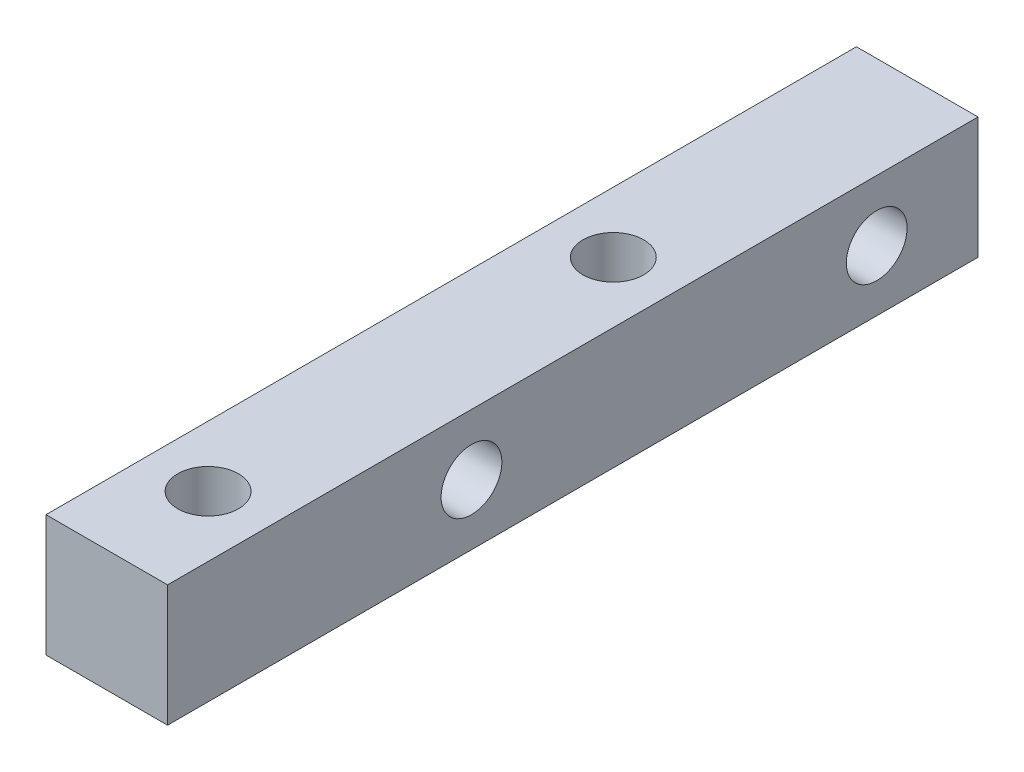
SolidWorks part; units mm, degrees
material "延性铁"
ref_plane "前视基准面" through (0, 0, 0) normal (0, 0, 1) x (1, 0, 0)
ref_plane "上视基准面" through (0, 0, 0) normal (0, 1, 0) x (1, 0, 0)
ref_plane "右视基准面" through (0, 0, 0) normal (1, 0, 0) x (0, 0, -1)
sketch "草图1" plane through (0, 0, 0) normal (0, 0, 1) x (1, 0, 0)
  line L1 (-3, 3) -> (3, 3)
  line L2 (-3, 3) -> (-3, -3)
  line L3 (-3, -3) -> (3, -3)
  line L4 (3, 3) -> (3, -3)
  line L5 (-3, 3) -> (3, -3) construction
  line L6 (-3, -3) -> (3, 3) construction
  point P0 (0, 0)
  dimension "D1" = 6
  dimension "D2" = 6
extrude "凸台-拉伸1" add sketch "草图1" along normal blind 40
sketch "草图2" plane through (-3, 0, 0) normal (-1, 0, 0) x (0, 0, 1)
  line L0 (0, 3) -> (0, -3) construction
  circle A0 centre (5, 0) radius 1.5
  circle A1 centre (25, 0) radius 1.5
  dimension "D1" = 20
  dimension "D2" = 5
extrude "切除-拉伸1" cut sketch "草图2" against normal through all
sketch "草图3" plane through (0, 3, 0) normal (0, 1, 0) x (1, 0, 0)
  line L0 (3, -40) -> (-3, -40) construction
  circle A0 centre (0, -15) radius 1.5
  circle A1 centre (0, -35) radius 1.5
  dimension "D1" = 5
  dimension "D2" = 20
extrude "切除-拉伸2" cut sketch "草图3" against normal through all
